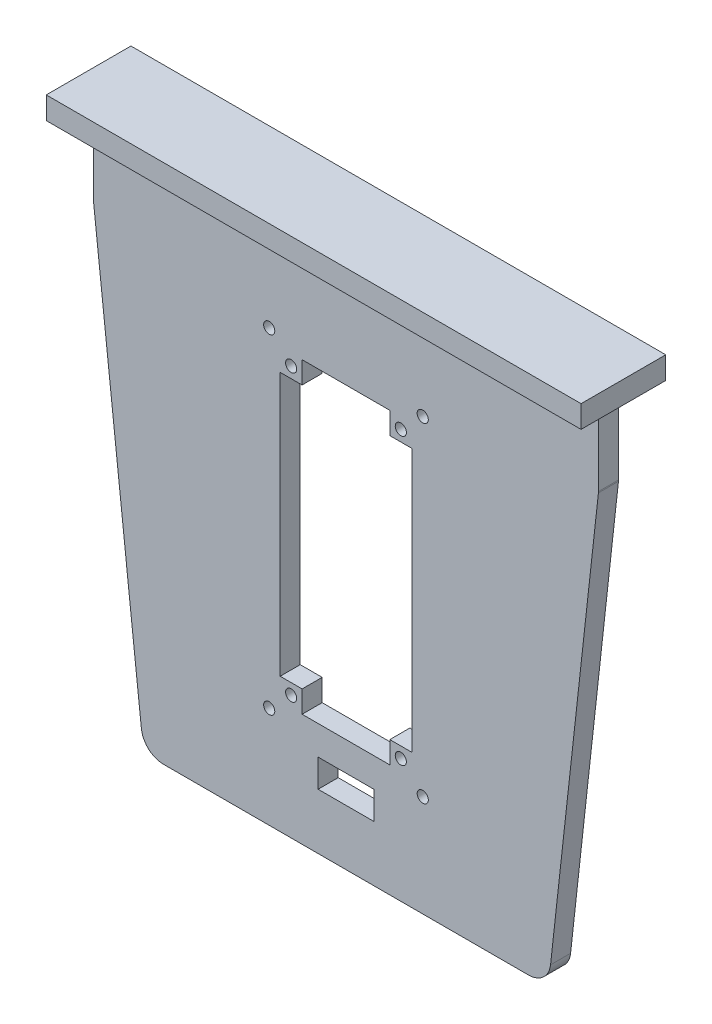
SolidWorks part; units mm, degrees
ref_plane "Front Plane" through (0, 0, 0) normal (0, 0, 1) x (1, 0, 0)
ref_plane "Top Plane" through (0, 0, 0) normal (0, 1, 0) x (1, 0, 0)
ref_plane "Right Plane" through (0, 0, 0) normal (1, 0, 0) x (0, 0, -1)
sketch "Sketch2" plane through (0, 0, 0) normal (0, 0, -1) x (-1, 0, 0)
  line L0 (-4.9216, 54.5793) -> (-4.9216, -59.013) construction
  line L6 (-62.4874, 48.8485) -> (52.6441, 48.8485)
  line L7 (52.6441, 48.8485) -> (41.7132, -49.932)
  line L8 (36.664, -54.4533) -> (-46.5073, -54.4533)
  line L9 (-62.4874, 48.8485) -> (-51.5564, -49.932)
  arc A4 (41.7132, -49.932) -> (36.664, -54.4533) centre (36.664, -49.3733) cw
  arc A5 (-51.5564, -49.932) -> (-46.5073, -54.4533) centre (-46.5073, -49.3733) ccw
  point P27 (-4.9216, -54.4533)
  point P28 (-4.9216, 48.8485)
  dimension "D4" = 98.7805
  dimension "D6" = 48.8485
  dimension "D11" = 5.08
  dimension "D2" = 115.1315
  dimension "D3" = 83.1712
  dimension "D5" = 36.664
extrude "Boss-Extrude1" add sketch "Sketch2" along normal blind 4.572
sketch "Sketch3" plane through (0, 48.8485, 0) normal (0, 1, 0) x (1, 0, 0)
  line L0 (-52.6441, 4.572) -> (-52.6441, 0)
  line L1 (-52.6441, 4.572) -> (62.4874, 4.572)
  line L2 (-52.6441, 0) -> (62.4874, 0)
  line L3 (62.4874, 4.572) -> (62.4874, 0)
  line L4 (62.4874, 4.572) -> (62.4874, 0) construction
  dimension "D1" = 0
extrude "Boss-Extrude2" add sketch "Sketch3" along normal blind 17.78
sketch "Sketch4" plane through (0, 66.6285, 0) normal (0, 1, 0) x (1, 0, 0)
  line L0 (-52.6441, 0) -> (62.4874, 0) construction
  line L1 (62.4874, 0) -> (62.4874, 4.572) construction
  line L2 (-52.6441, 0) -> (62.4874, 0) construction
  line L3 (62.4874, -7.366) -> (62.4874, 11.938) construction
  line L4 (-52.6441, -7.366) -> (-52.6441, 37.8542) construction
  line L5 (0, -33.6753) -> (0, 37.8542) construction
  line L10 (-56.0384, 11.938) -> (-56.0384, -7.366)
  line L11 (-56.0384, 11.938) -> (82.2468, 11.938) construction
  line L12 (62.4874, -7.366) -> (-56.0384, -7.366) construction
  line L13 (-56.0384, 11.938) -> (65.8816, 11.938)
  line L14 (-56.0384, -7.366) -> (65.8816, -7.366)
  line L15 (65.8816, 11.938) -> (65.8816, -7.366)
  line L16 (62.4874, 4.572) -> (-52.6441, 4.572) construction
  dimension "D1" = 7.366
  dimension "D2" = 7.366
  dimension "D3" = 3.3942
  dimension "D4" = 3.3942
fillet "Fillet1" radius 2.54 2 edges at (62.4874, 48.8485, -2.286) (-52.6441, 48.8485, -2.286)
extrude "Boss-Extrude4" add sketch "Sketch4" along normal blind 5.08
sketch "Sketch5" plane through (0, 0, -4.572) normal (0, 0, -1) x (-1, 0, 0)
  line L0 (-4.9216, 66.6285) -> (-4.9216, -54.4533) construction
  line L2 (-65.8816, 66.6285) -> (56.0384, 66.6285) construction
  line L3 (-46.5073, -54.4533) -> (36.664, -54.4533) construction
  line L4 (1.4284, -35.4033) -> (-11.2716, -35.4033)
  line L5 (-11.2716, -35.4033) -> (-11.2716, -41.7533)
  line L6 (-11.2716, -41.7533) -> (1.4284, -41.7533)
  line L7 (1.4284, -35.4033) -> (1.4284, -41.7533)
  point P11 (-4.9216, -41.7533)
  point P12 (-4.9216, -35.4033)
  dimension "D1" = 6.35
  dimension "D2" = 6.35
  dimension "D3" = 12.7
extrude "Cut-Extrude1" cut sketch "Sketch5" against normal blind 5.08
sketch "Sketch6" plane through (0, 0, -4.572) normal (0, 0, -1) x (-1, 0, 0)
  line L0 (-4.9216, 66.6285) -> (-4.9216, -54.4533) construction
  line L1 (-65.8816, 66.6285) -> (56.0384, 66.6285) construction
  line L2 (-46.5073, -54.4533) -> (36.664, -54.4533) construction
  line L3 (47.9122, 6.0876) -> (-57.7555, 6.0876) construction
  line L4 (-62.4874, 66.6285) -> (52.6441, 66.6285) construction
  line L5 (41.7132, -49.932) -> (52.6287, 48.7092) construction
  line L6 (10.0784, 41.2285) -> (10.0784, -28.7715)
  line L7 (-62.472, 48.7092) -> (-51.5564, -49.932) construction
  line L8 (10.0784, 41.2285) -> (-19.9216, 41.2285)
  line L9 (-19.9216, 41.2285) -> (-19.9216, -28.7715)
  line L10 (-19.9216, -28.7715) -> (10.0784, -28.7715)
  line L11 (-19.9216, 41.2285) -> (-19.9216, 36.2285)
  line L12 (-19.9216, 41.2285) -> (-14.9216, 41.2285)
  line L13 (-19.9216, 36.2285) -> (-14.9216, 36.2285)
  line L14 (-14.9216, 41.2285) -> (-14.9216, 36.2285)
  line L15 (5.0784, 41.2285) -> (5.0784, 36.2285)
  line L16 (10.0784, 36.2285) -> (5.0784, 36.2285)
  line L17 (-19.9216, 6.2285) -> (10.0784, 6.2285) construction
  line L18 (10.0784, -23.7715) -> (5.0784, -23.7715)
  line L19 (5.0784, -28.7715) -> (5.0784, -23.7715)
  line L20 (-19.9216, -23.7715) -> (-14.9216, -23.7715)
  line L21 (-14.9216, -28.7715) -> (-14.9216, -23.7715)
  line L22 (-17.4216, 36.2285) -> (-17.4216, 41.2285) construction
  line L23 (-14.9216, 38.7285) -> (-19.9216, 38.7285) construction
  line L24 (-19.9216, -23.7715) -> (-24.9216, -23.7715) construction
  line L25 (-24.9216, -23.7715) -> (-24.9216, -33.7715) construction
  line L26 (-24.9216, -28.7715) -> (-19.9216, -28.7715) construction
  line L27 (-22.4216, -28.7715) -> (-22.4216, -33.8515) construction
  circle A0 centre (-17.4216, 38.7285) radius 1.27
  circle A1 centre (7.5784, 38.7285) radius 1.27
  circle A2 centre (-17.4216, -26.2715) radius 1.27
  circle A3 centre (7.5784, -26.2715) radius 1.27
  circle A4 centre (-22.4216, -31.3115) radius 1.27
  circle A5 centre (12.5784, -31.3115) radius 1.27
  circle A6 centre (12.5784, 43.7685) radius 1.27
  circle A7 centre (-22.4216, 43.7685) radius 1.27
  point P19 (-4.9216, -28.7715)
  point P20 (-4.9216, 41.2285)
  dimension "D7" = 2.54
  dimension "D10" = 2.54
  dimension "D11" = 2.54
  dimension "D1" = 60.5409
  dimension "D2" = 15
  dimension "D3" = 70
  dimension "D4" = 25.4
  dimension "D5" = 5
  dimension "D6" = 5
  dimension "D8" = 5
  dimension "D9" = 10
extrude "Cut-Extrude2" cut sketch "Sketch6" against normal blind 6.35 contours L21 L10 L19 L18 L6 L16 L15 L8 L14 L13 L9 L20 | A0 | A3 | A2 | A4 | A5 | A6 | A7 | A1
